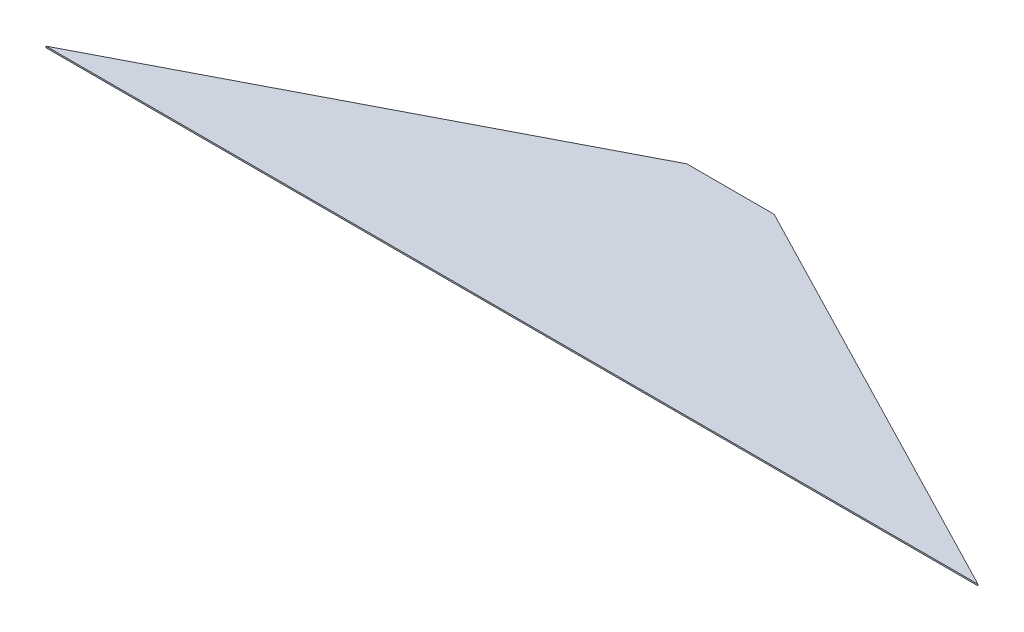
SolidWorks part; units mm, degrees
ref_plane "Front Plane" through (0, 0, 0) normal (0, 0, 1) x (1, 0, 0)
ref_plane "Top Plane" through (0, 0, 0) normal (0, 1, 0) x (1, 0, 0)
ref_plane "Right Plane" through (0, 0, 0) normal (1, 0, 0) x (0, 0, -1)
sketch "Sketch1" plane through (0, 0, 0) normal (0, 1, 0) x (1, 0, 0)
  line L0 (0, 0) -> (640, 0)
  line L1 (640, 0) -> (350, 150)
  line L2 (350, 150) -> (290, 150)
  line L3 (290, 150) -> (0, 0)
  line L4 (320, 150) -> (320, 0) construction
  dimension "D1" = 150
  dimension "D2" = 640
  dimension "D3" = 60
extrude "Boss-Extrude1" add sketch "Sketch1" along normal blind 1
